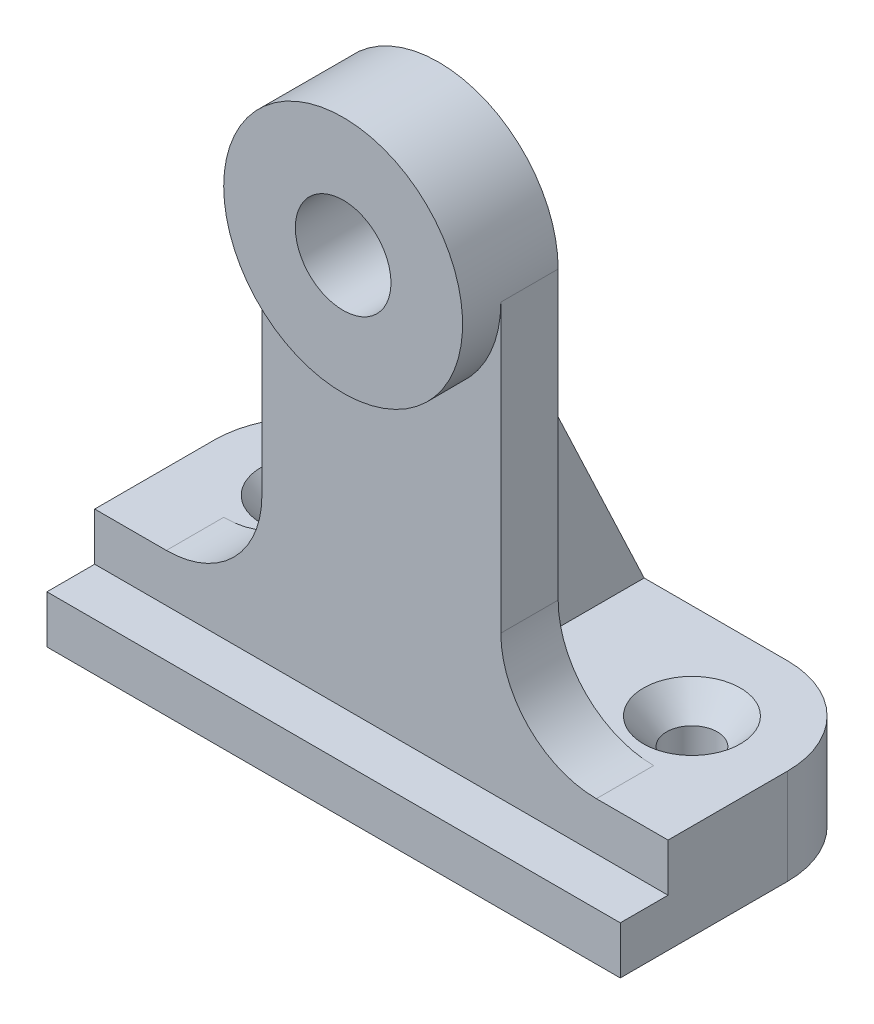
SolidWorks part; units mm, degrees
ref_plane "Front Plane" through (0, 0, 0) normal (0, 0, 1) x (1, 0, 0)
ref_plane "Top Plane" through (0, 0, 0) normal (0, 1, 0) x (1, 0, 0)
ref_plane "Right Plane" through (0, 0, 0) normal (1, 0, 0) x (0, 0, -1)
sketch "Sketch1" plane through (0, 0, 0) normal (0, 1, 0) x (1, 0, 0)
  line L0 (0, 42.3436) -> (0, -11.1125) construction
  line L1 (-25.4, 17.4625) -> (25.4, 17.4625)
  line L2 (-38.1, 4.7625) -> (-38.1, -11.1125)
  line L4 (38.1, 4.7625) -> (38.1, -11.1125)
  line L5 (-80.2591, 0) -> (81.5506, 0) construction
  line L6 (-38.1, -11.1125) -> (38.1, -11.1125)
  arc A0 (25.4, 17.4625) -> (38.1, 4.7625) centre (25.4, 4.7625) cw
  arc A1 (-25.4, 17.4625) -> (-38.1, 4.7625) centre (-25.4, 4.7625) ccw
  point P6 (38.1, 17.4625)
  dimension "D3" = 12.7
  dimension "D1" = 28.575
extrude "Boss-Extrude4" add sketch "Sketch1" along normal blind 12.7
sketch "Sketch10" plane through (0, 0, 0) normal (0, 1, 0) x (1, 0, 0)
  line L1 (-38.1, -11.1125) -> (38.1, -11.1125)
  line L2 (-38.1, -11.1125) -> (-38.1, -17.4625)
  line L3 (-38.1, -17.4625) -> (38.1, -17.4625)
  line L4 (38.1, -11.1125) -> (38.1, -17.4625)
  dimension "D1" = 76.2
  dimension "D2" = 6.35
extrude "Boss-Extrude5" add sketch "Sketch10" along normal blind 6.35
hole_wizard "CSK for 1/4 Flat Head Machine Screw1" positions "Sketch15" profile "Sketch16" countersink size "1/4" standard "ANSI Inch" end condition through all
sketch "Sketch15" plane through (0, 12.7, 0) normal (0, 1, 0) x (1, 0, 0)
  point P0 (-25.4, 4.7625)
  point P3 (25.4, 4.7625)
sketch "Sketch16" plane through (-25.4, 12.7, -4.7625) normal (1, 0, 0) x (0, 0, 1)
  line L0 (0, 0) -> (0, 12.7)
  line L1 (0, 12.7) -> (3.3782, 12.7)
  line L2 (3.3782, 12.7) -> (3.3782, 3.5209)
  line L3 (3.3782, 3.5209) -> (6.4389, 0)
  line L5 (6.4389, 0) -> (0, 0)
  line L6 (-3.3782, 3.5209) -> (-6.4389, 0) construction
  line L11 (0, -6.35) -> (0, 107.95) construction
  dimension "Thru Hole Dia." = 6.7564
  dimension "Thru Hole Depth" = 12.7
  dimension "Near C'Sink Dia." = 12.8778
  dimension "Near C'Sink Angle" = 82
sketch "Sketch19" plane through (0, 0, 11.1125) normal (0, 0, 1) x (1, 0, 0)
  line L0 (0, 0) -> (0, 47.625) construction
  line L1 (-38.1, 12.7) -> (38.1, 12.7) construction
  line L2 (-15.875, 12.7) -> (15.875, 12.7)
  line L3 (-15.875, 12.7) -> (-15.875, 63.5)
  line L5 (15.875, 12.7) -> (15.875, 63.5)
  arc A1 (-15.875, 63.5) -> (15.875, 63.5) centre (0, 63.5) ccw
  dimension "D2" = 31.75
  dimension "D3" = 31.75
extrude "Boss-Extrude6" add sketch "Sketch19" against normal blind 7.62
fillet "Fillet1" radius 12.7 2 edges at (15.875, 12.7, 7.3025) (-15.875, 12.7, 7.3025)
sketch "Sketch20" plane through (0, 0, 3.4925) normal (0, 0, -1) x (-1, 0, 0)
  circle A0 centre (0, 63.5) radius 15.875
  circle A1 centre (0, 63.5) radius 6.35
  dimension "D1" = 31.75
  dimension "D2" = 12.7
extrude "Boss-Extrude7" add sketch "Sketch20" against normal blind 12.7
sketch "Sketch21" plane through (0, 0, 0) normal (1, 0, 0) x (0, 0, -1)
  line L0 (-3.4925, 57.15) -> (17.4625, 12.7)
  line L1 (-3.4925, 25.4) -> (-3.4925, 63.5) construction
  line L2 (17.4625, 12.7) -> (4.7625, 12.7) construction
  line L3 (-3.4925, 57.15) -> (-3.4925, 12.7)
  line L4 (-3.4925, 12.7) -> (17.4625, 12.7)
  point P6 (16.8455, 12.7)
  dimension "D1" = 20.955
  dimension "D2" = 44.45
extrude "Boss-Extrude8" add sketch "Sketch21" along normal mid plane 12.7
